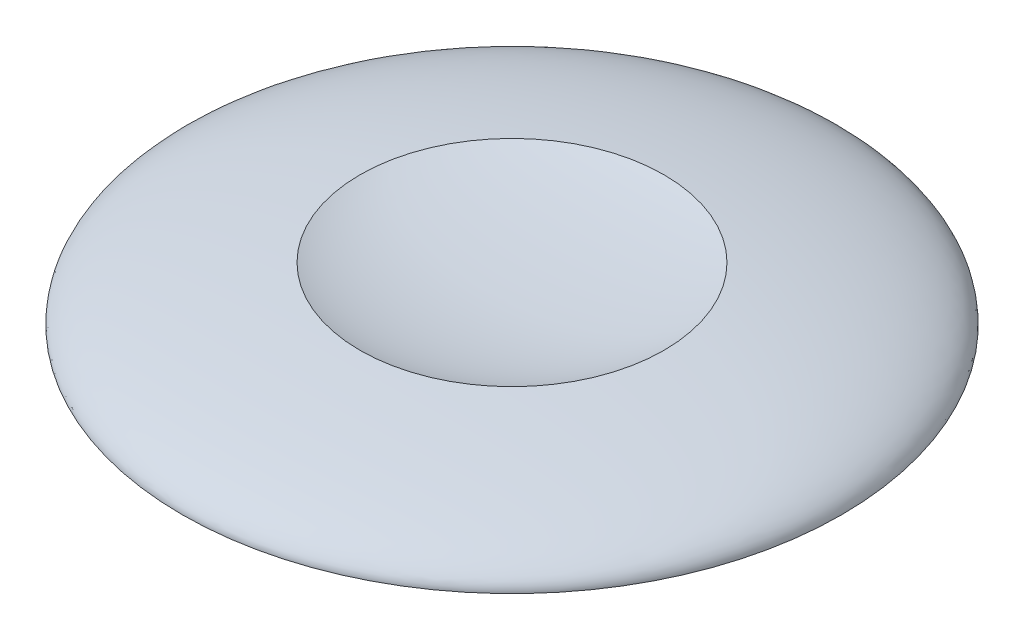
SolidWorks part; units mm, degrees
ref_plane "Front" through (0, 0, 0) normal (0, 0, 1) x (1, 0, 0)
ref_plane "Top" through (0, 0, 0) normal (0, 1, 0) x (1, 0, 0)
ref_plane "Right" through (0, 0, 0) normal (1, 0, 0) x (0, 0, -1)
sketch "Sketch1" plane through (0, 0, 0) normal (1, 0, 0) x (0, 0, -1)
  line L0 (1.7, 0) -> (5, 0)
  line L1 (0, 0.5114) -> (0, -3)
  line L2 (0.7, -0.1) -> (0.7, -2.9)
  line L3 (0, -3) -> (0.6, -3)
  line L4 (0.7, -0.1) -> (1.7, -0.1)
  line L5 (1.7, -0.1) -> (1.7, 0)
  arc A1 (0.7, -2.9) -> (0.6, -3) centre (0.6, -2.9) cw
  ellipse E1 centre (0, 1.1418) end of major axis (2.7023, 1.1418) minor radius 0.6304 (0, 0.5114) -> (2.3056, 0.813) ccw
  ellipse E2 centre (0, 0) end of major axis (5, 0) minor radius 0.9162 (5, 0) -> (2.3056, 0.813) ccw
  dimension "D1" = 1
  dimension "D2" = 0.7
  dimension "D3" = 5
revolve "Revolve1" add sketch "Sketch1" angle 360 about L1
